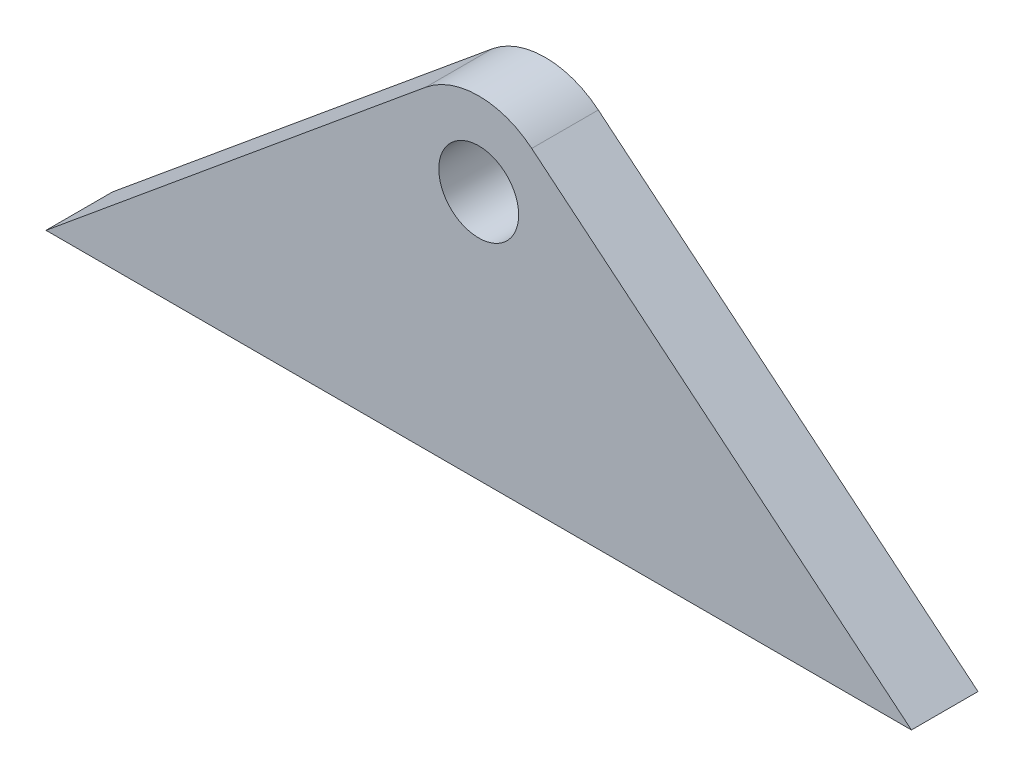
SolidWorks part; units mm, degrees
ref_plane "Alzado" through (0, 0, 0) normal (0, 0, 1) x (1, 0, 0)
ref_plane "Planta" through (0, 0, 0) normal (0, 1, 0) x (1, 0, 0)
ref_plane "Vista lateral" through (0, 0, 0) normal (1, 0, 0) x (0, 0, -1)
sketch "Croquis1" plane through (0, 0, 0) normal (0, 0, 1) x (1, 0, 0)
  line L0 (0, 0) -> (0, 75) construction
  line L1 (130, 0) -> (-130, 0)
  line L2 (-130, 0) -> (-15.9256, 94.2711)
  line L3 (130, 0) -> (15.9256, 94.2711)
  arc A0 (15.9256, 94.2711) -> (-15.9256, 94.2711) centre (0, 75) ccw
  circle A1 centre (0, 75) radius 12
  dimension "D3" = 25
  dimension "D4" = 24
  dimension "D1" = 260
  dimension "D2" = 75
extrude "Saliente-Extruir1" add sketch "Croquis1" along normal mid plane 20
